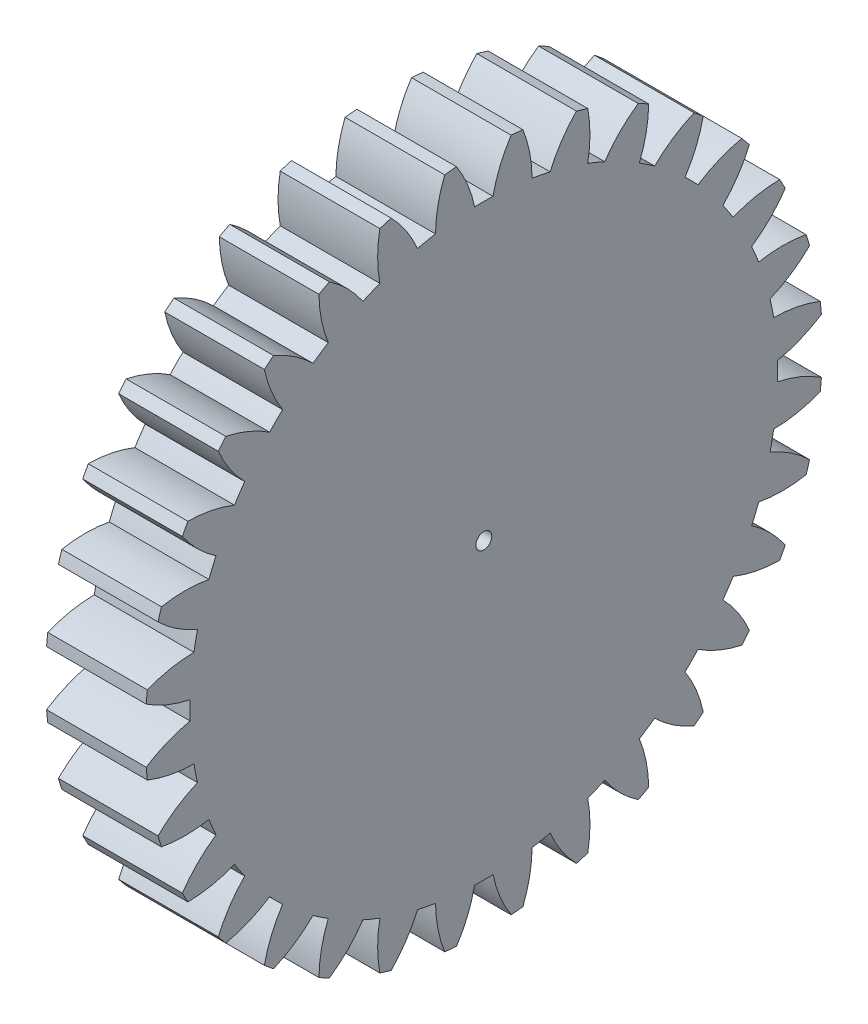
SolidWorks part; units mm, degrees
ref_plane "Plane1" through (0, 0, 0) normal (0, 0, 1) x (1, 0, 0)
ref_plane "Plane2" through (0, 0, 0) normal (0, 1, 0) x (1, 0, 0)
ref_plane "Plane3" through (0, 0, 0) normal (1, 0, 0) x (0, 0, -1)
other "Configuration Table"
sketch "HoldingSke" plane through (0, 0, 0) normal (0, 1, 0) x (1, 0, 0)
  line L0 (0, 0) -> (0.848, -0.5299)
  line L1 (-15, 0) -> (100, 0) construction
  line L2 (0, 0) -> (-2.1039, 2.3779)
  line L3 (0, 0) -> (-11.863, 4.5341)
  line L4 (0, 0) -> (7.3237, 4.5764)
  line L5 (0, 0) -> (-46.8476, -17.4728)
  line L6 (0, 0) -> (-4.1448, -2.7965)
  line L7 (-2.1039, 2.3779) -> (8.6586, 51.2059)
  line L8 (-76.2, 54.61) -> (-76.1, 54.61)
  line L9 (-71.009, 38.7566) -> (-53.1078, 45.2721)
  line L10 (-76.2, 71.12) -> (104.1128, 71.12)
  line L11 (0, 0) -> (-5, 0)
  line L12 (-76.2, 101.6) -> (-76.162, 101.6)
  line L13 (24.9733, 27.94) -> (52.9518, 28.4284)
  line L14 (24.9733, 27.94) -> (24.9743, 27.94)
  line L15 (24.9733, 27.94) -> (100.4006, 29.5858)
  line L16 (-63.627, -1) -> (-12.827, -1)
  circle A0 centre (0, 0) radius 0.4
  circle A1 centre (0, 0) radius 14.749
  circle A2 centre (0, 0) radius 37.5
  circle A3 centre (0, 0) radius 0.4
  dimension "MHD" = 29.498
  dimension "Hub_dia" = 75
  dimension "Bore" = 0.8
  dimension "MBD" = 0.8
  dimension "Num_teeth" = 32
  dimension "Pitch" = 1
  dimension "Overall_len" = 50
  dimension "Show_teeth" = 32
  dimension "Thickness" = 5
  dimension "OAL" = 50.0001
  dimension "T_dim" = 0.1
  dimension "Ap" = 20
  dimension "H" = 19.05
  dimension "Pitch_radius" = 180.3128
  dimension "Width" = 5
  dimension "Backlash" = 0.038
  dimension "Addendum_fac" = 1
  dimension "Dedendum_fac" = 1.25
  dimension "Clearance_fac" = 0.25
  dimension "Dedendum_add" = 0.001
  dimension "Module" = 1
sketch "BasProSke" plane through (0, 0, 0) normal (0, 1, 0) x (1, 0, 0)
  line L0 (-10, 0) -> (60, 0) construction
  line L1 (0, 0) -> (0, 17)
  line L2 (0, 0) -> (5, 0)
  line L3 (5, 0) -> (5, 17)
  line L4 (5, 17) -> (0, 17)
  dimension "Thickness" = 5
  dimension "Diameter" = 34
revolve "Base-Revolve" add sketch "BasProSke" angle 360 about L0
sketch "TooCutSke" plane through (0, 0, 0) normal (1, 0, 0) x (0, 0, -1)
  line L1 (0, 0) -> (0, 107) construction
  line L2 (0, 0) -> (-0.8516, 15.9773) construction
  line L3 (0, 0) -> (-3.1334, 31.8138) construction
  line L4 (-0.8516, 15.9773) -> (-1.5667, 15.9069) construction
  arc A0 (0.462, 14.7418) -> (-0.462, 14.7418) centre (0, 0) ccw
  arc A1 (1.3867, 16.9688) -> (-1.3867, 16.9688) centre (0, 0) ccw
  circle A2 centre (0, 0) radius 16 construction
  circle A3 centre (0, 0) radius 15.0351 construction
  arc A4 (-0.462, 14.7418) -> (-1.3867, 16.9688) centre (-6.7293, 13.4451) ccw
  arc A5 (1.3867, 16.9688) -> (0.462, 14.7418) centre (6.7293, 13.4451) ccw
  dimension "Root_dia" = 29.498
  dimension "Overcut_dia" = 34.0508
  dimension "Pitch_dia" = 32
  dimension "Base_dia" = 30.0702
  dimension "Flank_rad" = 6.4
  dimension "Half_ang" = 5.625
  dimension "Half_CT" = 0.7186
extrude "ToothCut" cut sketch "TooCutSke" along normal through all
fillet "Breaks" [suppressed] radius 0.02
fillet "RootFillets" [suppressed] radius 0.251
pattern_circular "TeethCuts" count 32 every 11.25 about axis through (-10, 0, 0) along (1, 0, 0) of "ToothCut", "RootFillets", "Breaks"
sketch "HubNeaOneSke" plane through (0, 0, 0) normal (-1, 0, 0) x (0, 0, 1)
  circle A0 centre (0, 0) radius 14.749
  dimension "Diameter" = 29.498
extrude "HubNearOne" [suppressed] add sketch "HubNeaOneSke" along normal blind 45.0001
sketch "HubNeaBotSke" plane through (0, 0, 0) normal (-1, 0, 0) x (0, 0, 1)
  circle A0 centre (0, 0) radius 14.749
  dimension "Diameter" = 29.498
extrude "HubNearBoth" [suppressed] add sketch "HubNeaBotSke" along normal blind 22.5
ref_plane "FarPln" through (5, 0, 0) normal (1, 0, 0) x (0, 0, -1)
sketch "HubFarSke" plane through (5, 0, 0) normal (1, 0, 0) x (0, 0, -1)
  circle A0 centre (0, 0) radius 14.749
  dimension "Diameter" = 29.498
extrude "HubFar" [suppressed] add sketch "HubFarSke" along normal blind 22.5
sketch "BorSke" plane through (0, 0, 0) normal (1, 0, 0) x (0, 0, -1)
  circle A0 centre (0, 0) radius 0.4
  dimension "Diameter" = 0.8
extrude "Bore" cut sketch "BorSke" along normal mid plane 100.0001
sketch "KeySke" plane through (0, 0, 0) normal (1, 0, 0) x (0, 0, -1)
  line L0 (-0.05, 0) -> (-0.05, 0.5)
  line L1 (-0.05, 0.5) -> (0.05, 0.5)
  line L2 (0.05, 0.5) -> (0.05, 0)
  line L3 (0, 0) -> (0, 34) construction
  line L4 (-0.05, 0) -> (0.05, 0)
  dimension "Offset" = 0.5
  dimension "Width" = 0.1
extrude "Keyway" [suppressed] cut sketch "KeySke" along normal mid plane 100.0001
pattern_circular "Keyway2" [suppressed] count 2 every 90 about axis through (-10, 0, 0) along (1, 0, 0)
equation "' \"Module@HoldingSke\" = 6.35"
equation "' \"Num_teeth@HoldingSke\" = 12"
equation "' \"Ap@HoldingSke\" =  20"
equation "' \"Ap@HoldingSke\" = 20"
equation "' \"Width@HoldingSke\" = 0.5 * 25.4"
equation "' \"Hub_dia@HoldingSke\"= 1 * 25.4"
equation "' \"Hub_dia@HoldingSke\" = 1 * 25.4"
equation "' \"Overall_len@HoldingSke\" = 1.0 * 25.4"
equation "' \"Bore@HoldingSke\" = 0.75 * 25.4"
equation "' \"T_dim@HoldingSke\" = 0.1 * 25.4"
equation "' \"Width@KeySke\" = 0.25 * 25.4"
equation "' \"Show_teeth@HoldingSke\" = 13"
equation "' \"Backlash@HoldingSke\" = 0.009 * 25.4"
equation "' \"Addendum_fac@HoldingSke\" = 1.0"
equation "' \"Dedendum_fac@HoldingSke\" = 1.25"
equation "' \"Dedendum_add@HoldingSke\" = 0.00005 * 25.4"
equation "' \"Clearance_fac@HoldingSke\" = 0.25"
equation "\"Pitch@HoldingSke\" = 1 / \"Module@HoldingSke\""
equation "\"Overcut_dia@TooCutSke\" = (\"Num_teeth@HoldingSke\" + 2 * \"Addendum_fac@HoldingSke\") / \"Pitch@HoldingSke\" + 0.002 * 25.4"
equation "\"Pitch_dia@TooCutSke\" = \"Num_teeth@HoldingSke\" / \"Pitch@HoldingSke\""
equation "\"Base_dia@TooCutSke\" = \"Num_teeth@HoldingSke\" / \"Pitch@HoldingSke\" * cos((\"Ap@HoldingSke\"  * 3.14159265 / 180))"
equation "\"Root_dia@TooCutSke\" = (\"Num_teeth@HoldingSke\" + 2) / \"Pitch@HoldingSke\" - 2 * (\"Addendum_fac@HoldingSke\" + \"Dedendum_fac@HoldingSke\") / \"Pitch@HoldingSke\" - \"Dedendum_add@HoldingSke\" * 2"
equation "\"Half_ang@TooCutSke\" = 180 / \"Num_teeth@HoldingSke\""
equation "\"Half_CT@TooCutSke\" = \"Num_teeth@HoldingSke\" / \"Pitch@HoldingSke\" * sin((3.14159265 / 2 / \"Num_teeth@HoldingSke\")) / 2 - 7 * \"Backlash@HoldingSke\" / 4"
equation "\"Flank_rad@TooCutSke\" = \"Num_teeth@HoldingSke\" / \"Pitch@HoldingSke\" / 5"
equation "\"Radius@RootFillets\" = \"Clearance_fac@HoldingSke\" / \"Pitch@HoldingSke\" + \"Dedendum_add@HoldingSke\""
equation "\"Break_rad@Breaks\" = 0.02 / \"Pitch@HoldingSke\""
equation "\"Thickness@HoldingSke\" = \"Width@HoldingSke\""
equation "\"OAL@HoldingSke\" = \"Thickness@HoldingSke\""
equation "\"MHD@HoldingSke\" = (\"Num_teeth@HoldingSke\" + 2) / \"Pitch@HoldingSke\" - 2 * (\"Addendum_fac@HoldingSke\" + \"Dedendum_fac@HoldingSke\")  / \"Pitch@HoldingSke\" - \"Dedendum_add@HoldingSke\" * 2"
equation "\"MBD@HoldingSke\" = (\"Num_teeth@HoldingSke\" + 2) / \"Pitch@HoldingSke\" - 2 * (\"Addendum_fac@HoldingSke\" + \"Dedendum_fac@HoldingSke\")  / \"Pitch@HoldingSke\" - \"Dedendum_add@HoldingSke\" * 2 - 0.002 * 25.4"
equation "\"MHD@HoldingSke\" = ((sgn( \"MHD@HoldingSke\" - \"Hub_dia@HoldingSke\" )-1)*( \"MHD@HoldingSke\" - \"Hub_dia@HoldingSke\" ))/-2+ \"Hub_dia@HoldingSke\""
equation "\"MBD@HoldingSke\" = ((sgn( \"MBD@HoldingSke\" - \"Bore@HoldingSke\" )-1)*( \"MBD@HoldingSke\" - \"Bore@HoldingSke\" ))/-2+ \"Bore@HoldingSke\""
equation "\"OAL@HoldingSke\" = ((sgn( \"OAL@HoldingSke\" - \"Overall_len@HoldingSke\" )+1)*( \"OAL@HoldingSke\" - \"Overall_len@HoldingSke\" ))/2 + \"Overall_len@HoldingSke\" + 0.000002 * 25.4"
equation "\"Num_teeth@TeethCuts\" = int( \"Show_teeth@HoldingSke\" ) + 1"
equation "\"Num_teeth@TeethCuts\" = ((sgn( \"Num_teeth@TeethCuts\" - \"Num_teeth@HoldingSke\" )-1)*( \"Num_teeth@TeethCuts\" - \"Num_teeth@HoldingSke\" ))/-2+ \"Num_teeth@HoldingSke\""
equation "\"Num_teeth@TeethCuts\" = ((sgn( \"Num_teeth@TeethCuts\" - 2.0)+1)*( \"Num_teeth@TeethCuts\" - 2.0))/2 +2.0"
equation "\"Angle@TeethCuts\" = 360.0 / \"Num_teeth@HoldingSke\""
equation "\"Diameter@BasProSke\" = (\"Num_teeth@HoldingSke\" + 2 * \"Addendum_fac@HoldingSke\") / \"Pitch@HoldingSke\""
equation "\"Thickness@BasProSke\"  = \"Thickness@HoldingSke\""
equation "' \"Fillet_rad@BasProSke\" =  \"Thickness@HoldingSke\" * 0.05"
equation "' \"Fillet_rad@BasProSke\" = \"Thickness@HoldingSke\" * 0.05"
equation "\"MHD@HoldingSke\" = ((sgn( \"MHD@HoldingSke\" - \"Root_dia@TooCutSke\" )-1)*( \"MHD@HoldingSke\" - \"Root_dia@TooCutSke\" ))/-2+ \"Root_dia@TooCutSke\""
equation "\"Diameter@HubNeaOneSke\" = \"MHD@HoldingSke\""
equation "\"Length@HubNearOne\" = \"OAL@HoldingSke\" - \"Thickness@BasProSke\""
equation "\"Diameter@HubNeaBotSke\" = \"MHD@HoldingSke\""
equation "\"Length@HubNearBoth\" = ( \"OAL@HoldingSke\" - \"Thickness@BasProSke\" ) / 2.0"
equation "\"Thickness@FarPln\" = \"Thickness@BasProSke\""
equation "\"Diameter@HubFarSke\" = \"MHD@HoldingSke\""
equation "\"Length@HubFar\" = ( \"OAL@HoldingSke\" - \"Thickness@BasProSke\" ) / 2.0"
equation "\"Diameter@BorSke\" = \"MBD@HoldingSke\""
equation "\"D1@Bore\" = \"OAL@HoldingSke\" * 2.0"
equation "\"D1@Keyway\" = \"OAL@HoldingSke\" * 2.0"
equation "\"Offset@KeySke\" = \"T_dim@HoldingSke\" + \"MBD@HoldingSke\" / 2.0"
